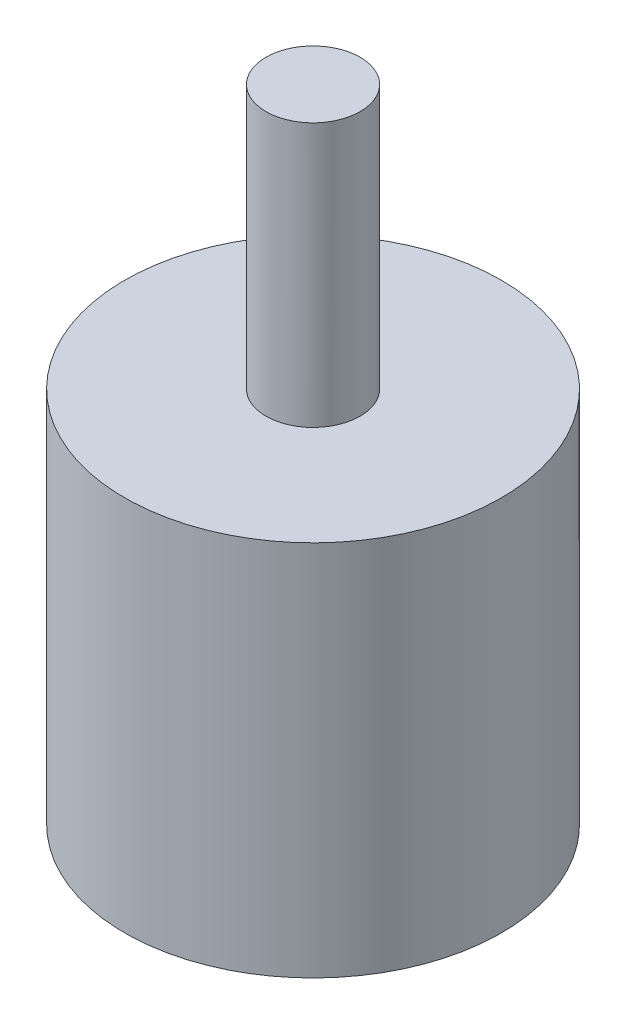
SolidWorks part; units mm, degrees
ref_plane "Front Plane" through (0, 0, 0) normal (0, 0, 1) x (1, 0, 0)
ref_plane "Top Plane" through (0, 0, 0) normal (0, 1, 0) x (1, 0, 0)
ref_plane "Right Plane" through (0, 0, 0) normal (1, 0, 0) x (0, 0, -1)
sketch "Sketch1" plane through (0, 0, 0) normal (0, 1, 0) x (1, 0, 0)
  circle A0 centre (0, 0) radius 3.175
  dimension "D1" = 6.35
extrude "Boss-Extrude1" add sketch "Sketch1" along normal blind 17.78
sketch "Sketch2" plane through (0, 0, 0) normal (0, -1, 0) x (1, 0, 0)
  circle A0 centre (0, 0) radius 12.7
  dimension "D1" = 25.4
extrude "Boss-Extrude2" add sketch "Sketch2" along normal blind 25.4
